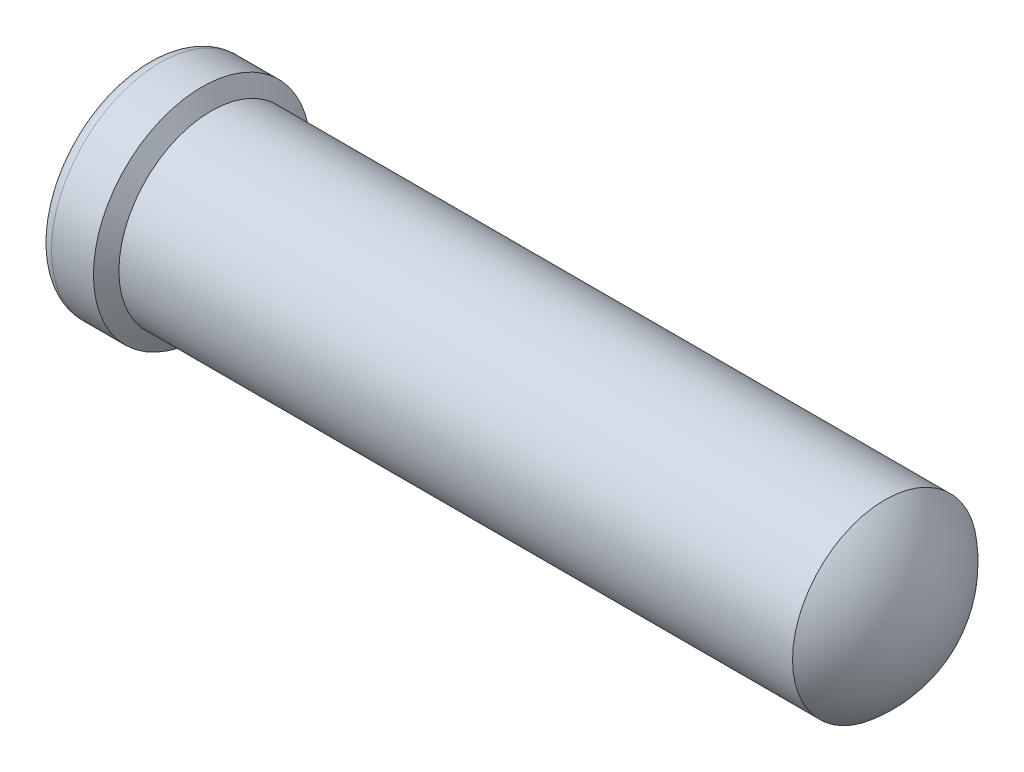
SolidWorks part; units mm, degrees
material "Brass Alloy 385"
ref_plane "Front Plane" through (0, 0, 0) normal (0, 0, 1) x (1, 0, 0)
ref_plane "Top Plane" through (0, 0, 0) normal (0, 1, 0) x (1, 0, 0)
ref_plane "Right Plane" through (0, 0, 0) normal (1, 0, 0) x (0, 0, -1)
sketch "Sketch1" plane through (0, 0, 0) normal (0, 0, 1) x (1, 0, 0)
  line L0 (0, 0) -> (0, 0.5474)
  line L1 (0.0762, 0.6236) -> (0.3175, 0.6236)
  line L2 (0.3175, 0.6236) -> (0.371, 0.5309)
  line L3 (4.2418, 0.5309) -> (0.371, 0.5309)
  line L5 (0, 0) -> (4.4958, 0)
  line L6 (0, 0) -> (4.4958, 0) construction
  arc A0 (4.4958, 0) -> (4.2418, 0.5309) centre (3.7847, -0.014) ccw
  arc A1 (0.0762, 0.6236) -> (0, 0.5474) centre (0.0762, 0.5474) ccw
  point P11 (0, 0.6236)
revolve "RevolutionAngle1" add sketch "Sketch1" angle 360 about L6
hole_wizard "Hole1" positions "Sketch3" profile "Sketch2" legacy
sketch "Sketch3" plane through (0, 0, 0) normal (-1, 0, 0) x (0, 0, 1)
  point P0 (0, 0)
sketch "Sketch2" plane through (0, 0, 0) normal (0, 1, 0) x (0, 0, 1)
  line L0 (0, 0) -> (0, 1.7987)
  line L1 (0, 1.7987) -> (0.4572, 1.524)
  line L2 (0.4572, 1.524) -> (0.4572, 0.0889)
  line L3 (0.4572, 0.0889) -> (0.5461, 0)
  line L4 (0.5461, 0) -> (0, 0)
  line L5 (0, -14.3089) -> (0, 102.4216) construction
  line L6 (0, 1.7987) -> (-0.4572, 1.524) construction
  line L7 (-0.4572, 0.0889) -> (-0.5461, 0) construction
  dimension "A" = 0.9144
  dimension "N" = 1.524
  dimension "B" = 1.0922
  dimension "P1" = 90
  dimension "Drill Angle" = 118
hole_wizard "Hole2" positions "3DSketch1" profile "Sketch4" legacy
sketch3d "3DSketch1"
  line L0 (0.3175, 0, 0) -> (0.0762, 0, 0) construction
  point P0 (0, 0, 0)
sketch "Sketch4" plane through (0, 0, 0) normal (0, 1, 0) x (0, 0, 1)
  line L0 (0, 0) -> (0, 2.2051)
  line L1 (0, 2.2051) -> (0.4572, 1.9304)
  line L2 (0.4572, 1.9304) -> (0.4572, 0.0889)
  line L3 (0.4572, 0.0889) -> (0.5461, 0)
  line L4 (0.5461, 0) -> (0, 0)
  line L5 (0, -14.3089) -> (0, 102.4216) construction
  line L6 (0, 2.2051) -> (-0.4572, 1.9304) construction
  line L7 (-0.4572, 0.0889) -> (-0.5461, 0) construction
  dimension "A" = 0.9144
  dimension "N" = 1.9304
  dimension "B" = 1.0922
  dimension "P1" = 90
  dimension "Drill Angle" = 118
ref_plane "Plane" through (0, 0, 0) normal (-1, 0, 0) x (0, 0, 1)
